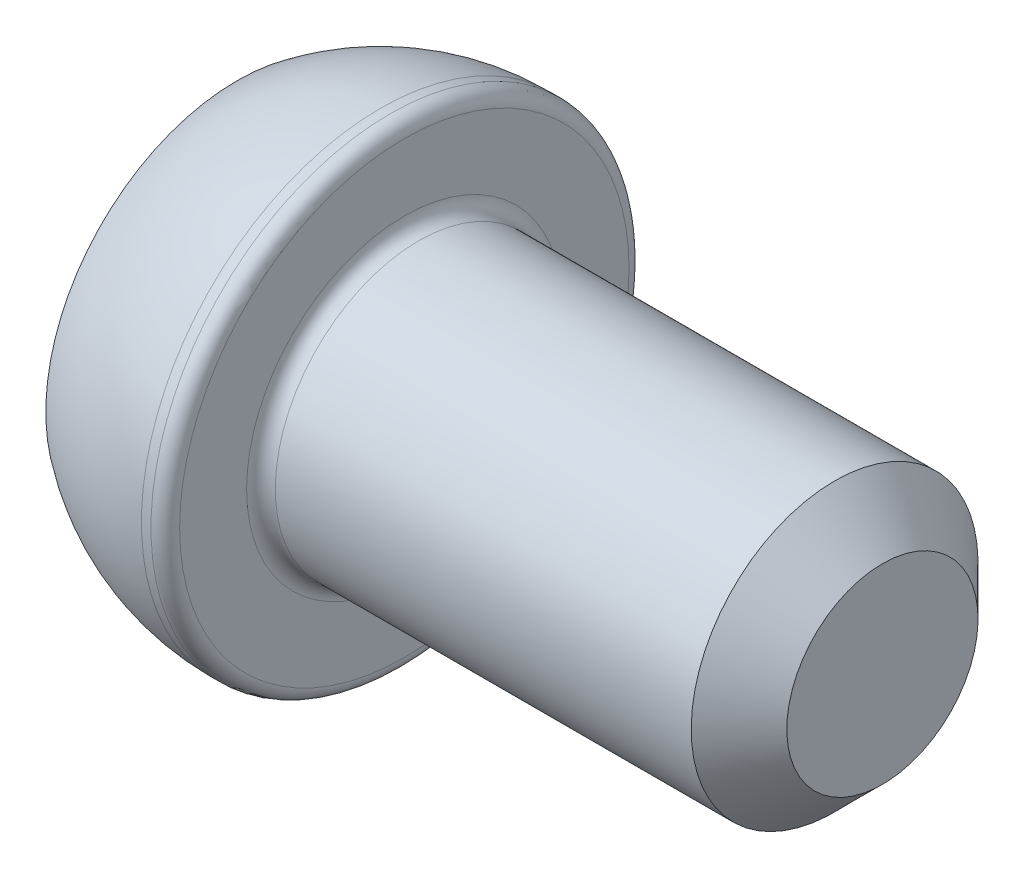
SolidWorks part; units mm, degrees
ref_plane "Спереди" through (0, 0, 0) normal (0, 0, 1) x (1, 0, 0)
ref_plane "Сверху" through (0, 0, 0) normal (0, 1, 0) x (1, 0, 0)
ref_plane "Справа" through (0, 0, 0) normal (1, 0, 0) x (0, 0, -1)
sketch "Эскиз1" plane through (0, 0, 0) normal (0, 0, 1) x (1, 0, 0)
  line L0 (0, 0) -> (0, 4)
  line L1 (3, 5) -> (3.5, 5)
  line L2 (3.5, 5) -> (3.5, 3)
  line L3 (3.5, 3) -> (13.5, 3)
  line L4 (13.5, 3) -> (13.5, 0)
  line L5 (13.5, 0) -> (0, 0) construction
  line L6 (0, 0) -> (13.5, 0)
  arc A0 (0, 4) -> (3, 5) centre (3, 0) cw
  point P9 (3.5, 4)
  dimension "D1" = 0.5
  dimension "D2" = 6
  dimension "D3" = 10
  dimension "D5" = 3.5
  dimension "D6" = 10
revolve "Повернуть1" add sketch "Эскиз1" angle 360 about L5
cosmetic thread "Условное изображение резьбы1" parameters "D2"=4.891
sketch "Эскиз2" plane through (0, 0, 0) normal (-1, 0, 0) x (0, 0, 1)
  line L1 (1.1547, 2) -> (-1.1547, 2)
  line L2 (-1.1547, 2) -> (-2.3094, 0)
  line L3 (-2.3094, 0) -> (-1.1547, -2)
  line L4 (-1.1547, -2) -> (1.1547, -2)
  line L5 (1.1547, -2) -> (2.3094, 0)
  line L6 (2.3094, 0) -> (1.1547, 2)
  circle A0 centre (0, 0) radius 2 construction
  dimension "D1" = 4
extrude "Вырез-Вытянуть1" cut sketch "Эскиз2" against normal blind 2
fillet "Скругление1" radius 0.3 2 edges at (3.5, 3, 0) (3.5, 5, 0)
chamfer "Фаска1" distance 1 angle 45 1 edges at (13.5, 3, 0)
